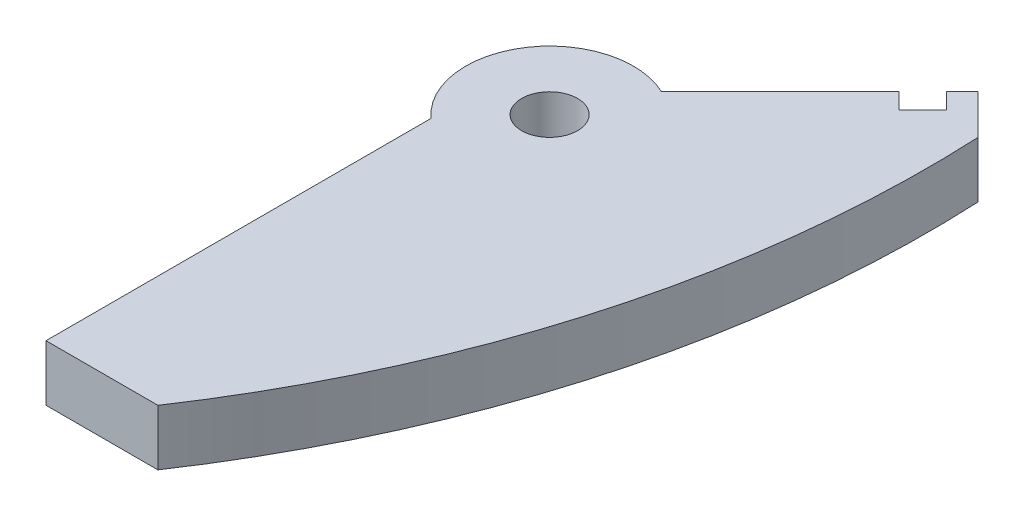
SolidWorks part; units mm, degrees
ref_plane "Front Plane" through (0, 0, 0) normal (0, 0, 1) x (1, 0, 0)
ref_plane "Top Plane" through (0, 0, 0) normal (0, 1, 0) x (1, 0, 0)
ref_plane "Right Plane" through (0, 0, 0) normal (1, 0, 0) x (0, 0, -1)
sketch "Sketch1" plane through (0, 0, 0) normal (0, 1, 0) x (1, 0, 0)
  line L0 (4.1049, 8.5951) -> (17.5753, 22.0654)
  line L1 (3.175, 0) -> (-3.175, 0)
  line L2 (6.35, -7.0995) -> (6.35, -50.8)
  line L3 (6.35, -50.8) -> (-6.35, -50.8)
  line L4 (-6.35, -7.0995) -> (-6.35, -50.8)
  line L5 (22.0654, 26.5556) -> (26.5556, 22.0654)
  line L6 (26.5556, 22.0654) -> (8.5951, 4.1049)
  line L7 (24.3105, 24.3105) -> (0, 0) construction
  line L8 (20.2694, 24.7595) -> (22.0654, 22.9635)
  line L9 (22.0654, 22.9635) -> (19.3714, 20.2694)
  line L10 (19.3714, 20.2694) -> (17.5753, 22.0654)
  line L11 (20.2694, 24.7595) -> (22.0654, 26.5556)
  circle A0 centre (0, 0) radius 3.175
  arc A1 (4.1049, 8.5951) -> (-6.35, -7.0995) centre (0, 0) ccw
  arc A2 (6.35, -7.0995) -> (8.5951, 4.1049) centre (0, 0) ccw
  arc A4 (26.5556, 22.0654) -> (6.35, -50.8) centre (-93.9156, 16.2379) cw
  dimension "D1" = 6.35
  dimension "D2" = 19.05
  dimension "D3" = 12.7
  dimension "D4" = 6.35
  dimension "D5" = 25.4
  dimension "D6" = 45
  dimension "D7" = 6.35
  dimension "D8" = 135
  dimension "D9" = 3.81
  dimension "D10" = 2.54
  dimension "D11" = 2.54
extrude "Boss-Extrude1" add sketch "Sketch1" along normal mid plane 6.35
